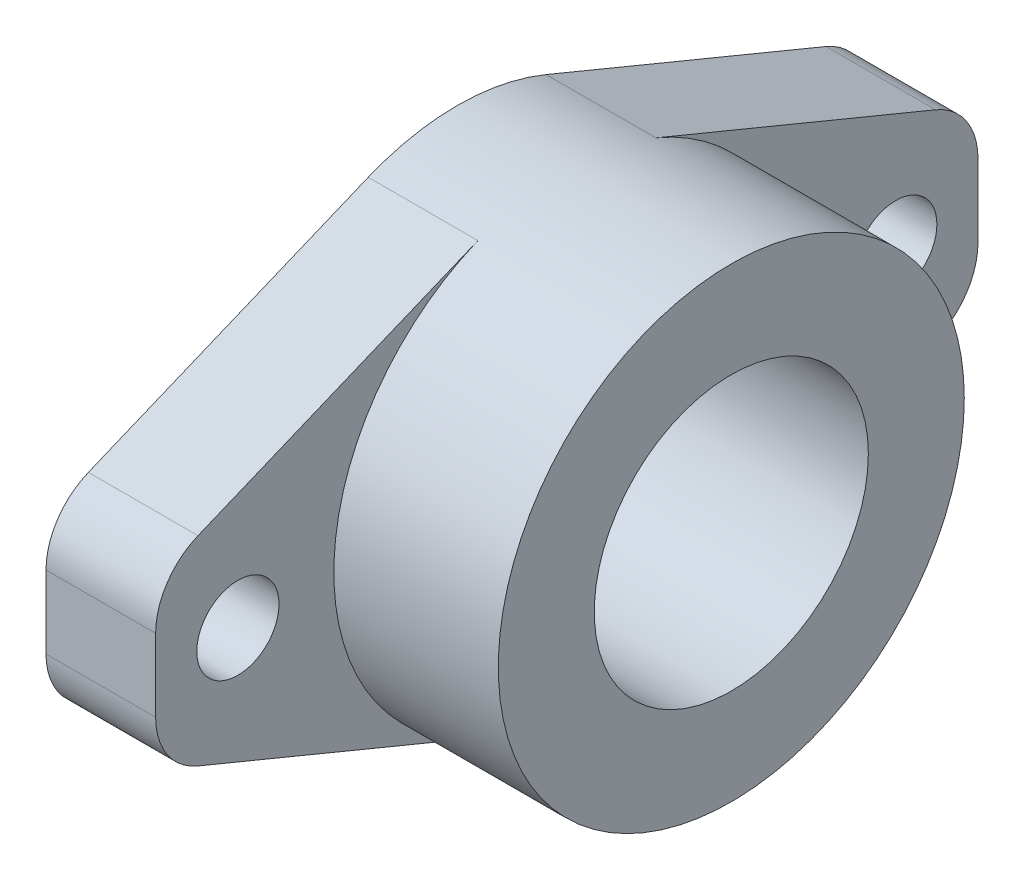
SolidWorks part; units mm, degrees
ref_plane "Front Plane" through (0, 0, 0) normal (0, 0, 1) x (1, 0, 0)
ref_plane "Top Plane" through (0, 0, 0) normal (0, 1, 0) x (1, 0, 0)
ref_plane "Right Plane" through (0, 0, 0) normal (1, 0, 0) x (0, 0, -1)
sketch "Sketch1" plane through (0, 0, 0) normal (1, 0, 0) x (0, 0, -1)
  line L0 (-24, 0) -> (0, 0) construction
  line L2 (30, -6) -> (30, 6)
  line L4 (-30, -6) -> (-30, 6)
  line L5 (30, -6) -> (-30, 6) construction
  line L6 (30, 6) -> (-30, -6) construction
  line L7 (0, 0) -> (24, 0) construction
  line L8 (-30, 6) -> (-6.4909, 15.712)
  line L9 (30, 6) -> (6.4909, 15.712)
  line L10 (-30, -6) -> (-6.4909, -15.712)
  line L11 (30, -6) -> (6.4909, -15.712)
  circle A0 centre (0, 0) radius 10
  arc A1 (-6.4909, -15.712) -> (6.4909, -15.712) centre (0, 0) ccw
  circle A2 centre (-24, 0) radius 3
  circle A3 centre (24, 0) radius 3
  arc A4 (6.4909, 15.712) -> (-6.4909, 15.712) centre (0, 0) ccw
  dimension "D1" = 20
  dimension "D3" = 6
  dimension "D2" = 24
  dimension "D4" = 60
  dimension "D5" = 12
extrude "Boss-Extrude1" add sketch "Sketch1" along normal blind 8
sketch "Sketch3" plane through (0, 0, 0) normal (1, 0, 0) x (0, 0, -1)
  circle A0 centre (0, 0) radius 10 construction
  circle A1 centre (0, 0) radius 10
  circle A2 centre (0, 0) radius 17
extrude "Boss-Extrude2" add sketch "Sketch3" along normal blind 20
fillet "Fillet1" radius 5 4 edges at (4, -6, 30) (4, 6, 30) (4, 6, -30) (4, -6, -30)
